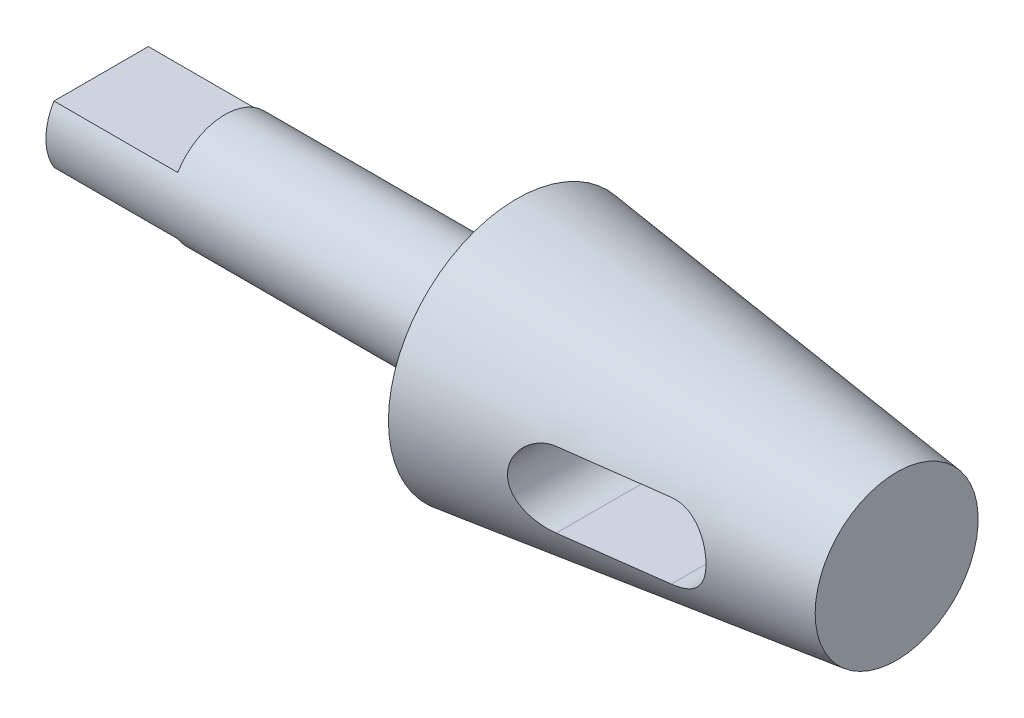
SolidWorks part; units mm, degrees
material "БрА9Мц2Л ГОСТ 493-79"
ref_plane "Спереди" through (0, 0, 0) normal (0, 0, 1) x (1, 0, 0)
ref_plane "Сверху" through (0, 0, 0) normal (0, 1, 0) x (1, 0, 0)
ref_plane "Справа" through (0, 0, 0) normal (1, 0, 0) x (0, 0, -1)
sketch "Эскиз2" plane through (0, 0, 0) normal (0, 0, 1) x (1, 0, 0)
  line L0 (-94, 12.5) -> (0, 12.5)
  line L1 (0, 12.5) -> (0, 29)
  line L2 (0, 29) -> (86, 18.4405)
  line L3 (86, 18.4405) -> (86, 0)
  line L5 (-94, 0) -> (86, 0)
  line L6 (0, 0) -> (86, 0) construction
  line L7 (-94, 12.5) -> (-94, 0)
  dimension "D1" = 180
  dimension "D3" = 94
  dimension "D4" = 58
  dimension "D5" = 7
  dimension "D6" = 25
revolve "Повернуть1" add sketch "Эскиз2" angle 360 about L6
sketch "Эскиз3" plane through (0, 0, 0) normal (0, 0, 1) x (1, 0, 0)
  line L0 (32.5, 0) -> (55.5, 0) construction
  line L1 (32.5, 8.5) -> (55.5, 8.5)
  line L2 (32.5, -8.5) -> (55.5, -8.5)
  line L3 (86, -18.4405) -> (86, 18.4405) construction
  line L4 (-94, -12.5) -> (-66, -12.5)
  line L5 (-94, -12.5) -> (0, -12.5) construction
  line L6 (-66, -12.5) -> (-66, -6.5)
  line L7 (-66, -6.5) -> (-94, -6.5)
  line L8 (-94, 12.5) -> (-94, -12.5) construction
  line L9 (-94, -6.5) -> (-94, -12.5)
  line L15 (-94, 0) -> (0, 0) construction
  line L16 (-94, 6.5) -> (-94, 12.5)
  line L17 (-94, 12.5) -> (-66, 12.5)
  line L18 (-66, 12.5) -> (-66, 6.5)
  line L19 (-66, 6.5) -> (-94, 6.5)
  arc A0 (32.5, 8.5) -> (32.5, -8.5) centre (32.5, 0) ccw
  arc A1 (55.5, -8.5) -> (55.5, 8.5) centre (55.5, 0) ccw
  point P2 (44, 0)
  point P8 (64, 0)
  point P11 (24, 0)
  dimension "D1" = 8.5
  dimension "D3" = 40
  dimension "D2" = 22
  dimension "D4" = 13
  dimension "D5" = 28
extrude "Вырез-Вытянуть1" cut sketch "Эскиз3" against normal through all both and the other way through all
fillet "Скругление1" radius 3 1 edges at (0, 0, 12.5)
